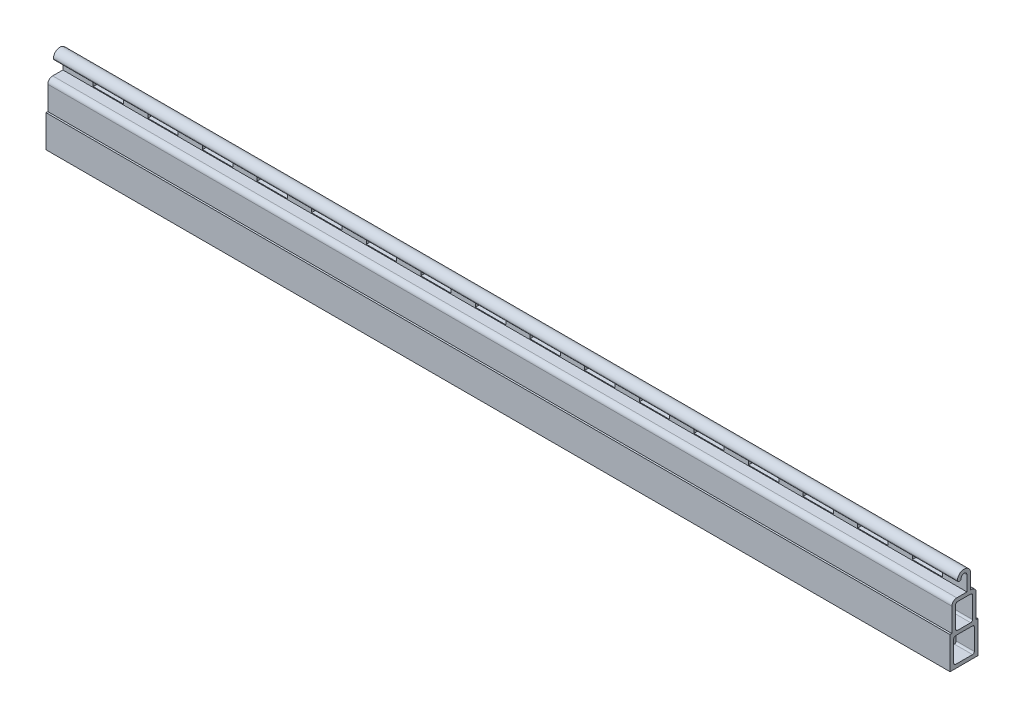
SolidWorks part; units mm, degrees
ref_plane "Plan de face" through (0, 0, 0) normal (0, 0, 1) x (1, 0, 0)
ref_plane "Plan de dessus" through (0, 0, 0) normal (0, 1, 0) x (1, 0, 0)
ref_plane "Plan de droite" through (0, 0, 0) normal (1, 0, 0) x (0, 0, -1)
sketch "Esquisse1" plane through (0, 0, 0) normal (1, 0, 0) x (0, 0, -1)
  line L0 (-7.1172, 2.5) -> (6.7495, 2.5) construction
  line L1 (4.3604, 2.8) -> (-7.1172, 2.8) construction
  line L2 (21.1727, 7.5) -> (-42.9122, 7.5) construction
  line L3 (-2.3262, 5.5148) -> (-2.3262, -4.9768) construction
  line L4 (-75, -4.7823) -> (-75, 49.585) construction
  line L5 (4.3604, 2.2) -> (-7.1172, 2.2) construction
  line L6 (-4.6262, 2.9917) -> (-4.6262, -2.9495) construction
  line L7 (-4.0262, -2.9495) -> (-4.0262, 2.9917) construction
  line L8 (-0.3262, 16.7097) -> (-0.3262, -10.2001) construction
  line L9 (-3.7262, 7.837) -> (-3.7262, 1.9485) construction
  line L10 (1.3082, 6.9) -> (-6.5961, 6.9) construction
  line L11 (-4.3262, 6.7) -> (-4.3262, 2.8)
  line L12 (-4.3262, 2.8) -> (-4.6262, 2.8)
  line L13 (-4.6262, 2.8) -> (-4.6262, -2.5)
  line L14 (-0.3262, 2.8) -> (-0.0262, 2.8)
  line L15 (-0.3262, 6.7) -> (-0.3262, 2.8)
  line L16 (-0.0262, 2.8) -> (-0.0262, -2.5)
  line L17 (-8.2562, -2.5) -> (6.7495, -2.5) construction
  line L18 (-7.1172, -1.9) -> (2.4185, -1.9) construction
  line L19 (-3.5262, 7.5) -> (-1.8462, 7.5)
  line L20 (-1.2462, 7.5) -> (-1.1262, 7.5)
  line L21 (-4.6262, -2.5) -> (-0.0262, -2.5)
  line L22 (-3.7262, 6.6) -> (-3.7262, 3.1)
  line L23 (-1.2462, 15.1007) -> (-1.2462, 5.976) construction
  line L24 (-3.4062, 15.0975) -> (-3.4062, 8.0497) construction
  line L25 (-1.8462, 15.9179) -> (-1.8462, 7.3015) construction
  line L26 (-2.8062, 15.0975) -> (-2.8062, 8.0497) construction
  line L27 (-4.3262, 14.9531) -> (-4.3262, -2.6693) construction
  line L28 (-6.339, 11) -> (4.0977, 11) construction
  line L29 (0.446, 9.92) -> (-4.6975, 9.92) construction
  line L30 (-1.2462, 9.92) -> (-1.2462, 7.5)
  line L31 (-4.0262, 1.9) -> (-4.0262, -1.6)
  line L32 (-1.8462, 7.5) -> (-1.8462, 9.92)
  line L33 (-3.1062, 9.419) -> (-3.1062, 10.1064) construction
  line L34 (-0.9262, 6.6) -> (-0.9262, 3.1)
  line L35 (-0.6262, 1.9) -> (-0.6262, -1.6)
  line L36 (-3.4262, 6.9) -> (-1.2262, 6.9)
  line L37 (-3.4262, 2.8) -> (-1.2262, 2.8)
  line L38 (-3.7262, 2.2) -> (-0.9262, 2.2)
  line L39 (-3.7262, -1.9) -> (-0.9262, -1.9)
  arc A0 (-4.0262, -1.6) -> (-3.7262, -1.9) centre (-3.7262, -1.6) ccw
  arc A1 (-0.6262, -1.6) -> (-0.9262, -1.9) centre (-0.9262, -1.6) cw
  arc A2 (-4.0262, 1.9) -> (-3.7262, 2.2) centre (-3.7262, 1.9) cw
  arc A3 (-0.6262, 1.9) -> (-0.9262, 2.2) centre (-0.9262, 1.9) ccw
  arc A4 (-0.9262, 6.6) -> (-1.2262, 6.9) centre (-1.2262, 6.6) ccw
  arc A5 (-0.9262, 3.1) -> (-1.2262, 2.8) centre (-1.2262, 3.1) cw
  arc A6 (-3.7262, 3.1) -> (-3.4262, 2.8) centre (-3.4262, 3.1) ccw
  arc A7 (-3.7262, 6.6) -> (-3.4262, 6.9) centre (-3.4262, 6.6) cw
  arc A8 (-0.3262, 6.7) -> (-1.1262, 7.5) centre (-1.1262, 6.7) ccw
  arc A9 (-4.3262, 6.7) -> (-3.5262, 7.5) centre (-3.5262, 6.7) cw
  arc A19 (-1.2462, 9.92) -> (-3.4062, 9.92) centre (-2.3262, 9.92) ccw
  arc A20 (-1.8462, 9.92) -> (-2.8062, 9.92) centre (-2.3262, 9.92) ccw
  arc A21 (-3.4062, 9.92) -> (-2.8062, 9.92) centre (-3.1062, 9.92) ccw
  point P45 (-4.0262, -1.9)
  point P48 (-0.6262, -1.9)
  point P51 (-4.0262, 2.2)
  point P54 (-0.6262, 2.2)
  point P57 (-0.9262, 6.9)
  point P61 (-0.9262, 2.8)
  point P64 (-3.7262, 2.8)
  point P67 (-3.7262, 6.9)
  point P78 (-0.3262, 7.5)
  point P81 (-4.3262, 7.5)
  dimension "D4" = 5
  dimension "D5" = 0.3
  dimension "D9" = 0.6
  dimension "D11" = 0.6
  dimension "D12" = 0.3
  dimension "D3" = 0.92
  dimension "D8" = 0.6
  dimension "D15" = 0.6
  dimension "D16" = 0.6
  dimension "D17" = 2
  dimension "D18" = 0.3
  dimension "D19" = 0.8
  dimension "D2" = 10
  dimension "D6" = 0.3
  dimension "D7" = 4
  dimension "D10" = 0.6
  dimension "D13" = 3.5
  dimension "D14" = 0.3
extrude "Boss.-Extru.1" add sketch "Esquisse1" along normal blind 149
sketch "Esquisse2" plane through (0, 0, 1.2462) normal (0, 0, -1) x (-1, 0, 0)
  line L0 (-19, 8.6336) -> (-19, 7.6336)
  line L2 (-19, 8.6336) -> (-14, 8.6336)
  line L3 (-14, 8.6336) -> (-14, 7.6336)
  line L4 (-19, 7.6336) -> (-14, 7.6336)
  line L6 (-28, 8.6336) -> (-28, 7.6336)
  line L7 (-28, 8.6336) -> (-23, 8.6336)
  line L8 (-23, 8.6336) -> (-23, 7.6336)
  line L9 (-28, 7.6336) -> (-23, 7.6336)
  line L10 (-37, 8.6336) -> (-37, 7.6336)
  line L11 (-37, 8.6336) -> (-32, 8.6336)
  line L12 (-32, 8.6336) -> (-32, 7.6336)
  line L13 (-37, 7.6336) -> (-32, 7.6336)
  line L14 (-46, 8.6336) -> (-46, 7.6336)
  line L15 (-46, 8.6336) -> (-41, 8.6336)
  line L16 (-41, 8.6336) -> (-41, 7.6336)
  line L17 (-46, 7.6336) -> (-41, 7.6336)
  line L18 (-55, 8.6336) -> (-55, 7.6336)
  line L19 (-55, 8.6336) -> (-50, 8.6336)
  line L20 (-50, 8.6336) -> (-50, 7.6336)
  line L21 (-55, 7.6336) -> (-50, 7.6336)
  line L22 (-64, 8.6336) -> (-64, 7.6336)
  line L23 (-64, 8.6336) -> (-59, 8.6336)
  line L24 (-59, 8.6336) -> (-59, 7.6336)
  line L25 (-64, 7.6336) -> (-59, 7.6336)
  line L26 (-73, 8.6336) -> (-73, 7.6336)
  line L27 (-73, 8.6336) -> (-68, 8.6336)
  line L28 (-68, 8.6336) -> (-68, 7.6336)
  line L29 (-73, 7.6336) -> (-68, 7.6336)
  line L30 (-82, 8.6336) -> (-82, 7.6336)
  line L31 (-82, 8.6336) -> (-77, 8.6336)
  line L32 (-77, 8.6336) -> (-77, 7.6336)
  line L33 (-82, 7.6336) -> (-77, 7.6336)
  line L34 (-91, 8.6336) -> (-91, 7.6336)
  line L35 (-91, 8.6336) -> (-86, 8.6336)
  line L36 (-86, 8.6336) -> (-86, 7.6336)
  line L37 (-91, 7.6336) -> (-86, 7.6336)
  line L38 (-100, 8.6336) -> (-100, 7.6336)
  line L39 (-100, 8.6336) -> (-95, 8.6336)
  line L40 (-95, 8.6336) -> (-95, 7.6336)
  line L41 (-100, 7.6336) -> (-95, 7.6336)
  line L42 (-109, 8.6336) -> (-109, 7.6336)
  line L43 (-109, 8.6336) -> (-104, 8.6336)
  line L44 (-104, 8.6336) -> (-104, 7.6336)
  line L45 (-109, 7.6336) -> (-104, 7.6336)
  line L46 (-118, 8.6336) -> (-118, 7.6336)
  line L47 (-118, 8.6336) -> (-113, 8.6336)
  line L48 (-113, 8.6336) -> (-113, 7.6336)
  line L49 (-118, 7.6336) -> (-113, 7.6336)
  line L50 (-127, 8.6336) -> (-127, 7.6336)
  line L51 (-127, 8.6336) -> (-122, 8.6336)
  line L52 (-122, 8.6336) -> (-122, 7.6336)
  line L53 (-127, 7.6336) -> (-122, 7.6336)
  line L54 (-136, 8.6336) -> (-136, 7.6336)
  line L55 (-136, 8.6336) -> (-131, 8.6336)
  line L56 (-131, 8.6336) -> (-131, 7.6336)
  line L57 (-136, 7.6336) -> (-131, 7.6336)
  line L58 (-145, 8.6336) -> (-145, 7.6336)
  line L59 (-145, 8.6336) -> (-140, 8.6336)
  line L60 (-140, 8.6336) -> (-140, 7.6336)
  line L61 (-145, 7.6336) -> (-140, 7.6336)
  line L79 (-10, 8.6336) -> (-10, 7.6336)
  line L80 (-10, 8.6336) -> (-5, 8.6336)
  line L81 (-5, 8.6336) -> (-5, 7.6336)
  line L82 (-10, 7.6336) -> (-5, 7.6336)
extrude "Enlèv. mat.-Extru.1" cut sketch "Esquisse2" against normal blind 10
ref_plane "Plan1" through (74.5, 0, 0) normal (1, 0, 0) x (0, 0, -1)
ref_plane "Plan2" through (3, 0, 0) normal (1, 0, 0) x (0, 0, -1)
sketch "Esquisse4" plane through (3, 0, 0) normal (1, 0, 0) x (0, 0, -1)
  line L1 (-0.8006, 6.9489) -> (-3.7909, 6.9489)
  line L2 (-0.8006, 6.9489) -> (-0.8006, 2.6859)
  line L3 (-0.8006, 2.6859) -> (-3.7909, 2.6859)
  line L4 (-3.7909, 6.9489) -> (-3.7909, 2.6859)
  line L5 (-0.5093, 2.3025) -> (-4.1589, 2.3025)
  line L6 (-0.5093, 2.3025) -> (-0.5093, -1.9911)
  line L7 (-0.5093, -1.9911) -> (-4.1589, -1.9911)
  line L8 (-4.1589, 2.3025) -> (-4.1589, -1.9911)
extrude "Boss.-Extru.3" add sketch "Esquisse4" along normal blind 0.8
mirror "Symétrie1" about plane through (74.5, 0, 0) normal (1, 0, 0) of "Boss.-Extru.3"
sketch "Esquisse5" plane through (0, 0, 0.0262) normal (0, 0, -1) x (-1, 0, 0)
  text T0 "www.a4.fr" font "Arial" height in points 14
extrude "Boss.-Extru.4" add sketch "Esquisse5" along normal blind 0.5
